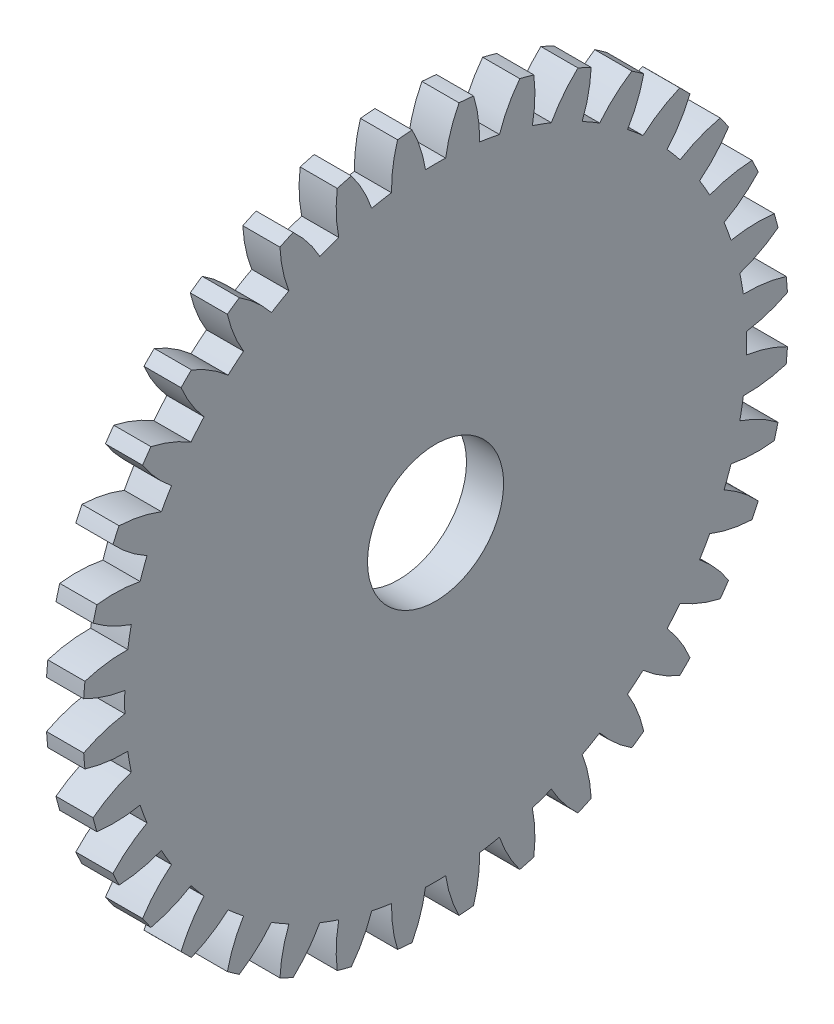
SolidWorks part; units mm, degrees
ref_plane "Plane1" through (0, 0, 0) normal (0, 0, 1) x (1, 0, 0)
ref_plane "Plane2" through (0, 0, 0) normal (0, 1, 0) x (1, 0, 0)
ref_plane "Plane3" through (0, 0, 0) normal (1, 0, 0) x (0, 0, -1)
other "Configuration Table"
sketch "HoldingSke" plane through (0, 0, 0) normal (0, 1, 0) x (1, 0, 0)
  line L0 (0, 0) -> (0.2697, -0.1959)
  line L1 (-15, 0) -> (100, 0) construction
  line L2 (0, 0) -> (-2.1039, 2.3779)
  line L3 (0, 0) -> (-11.863, 4.5341)
  line L4 (0, 0) -> (6.9867, 5.0761)
  line L5 (0, 0) -> (-46.8476, -17.4728)
  line L6 (0, 0) -> (-4.9738, -3.3558)
  line L7 (-2.1039, 2.3779) -> (8.6586, 51.2059)
  line L8 (-76.2, 54.61) -> (-72.9, 54.61)
  line L9 (-67.7845, 28.3722) -> (-49.3413, 33.142)
  line L10 (-76.2, 71.12) -> (104.1128, 71.12)
  line L11 (0, 0) -> (-6, 0)
  line L12 (-76.2, 101.6) -> (-76.093, 101.6)
  line L13 (24.9733, 27.94) -> (52.9518, 28.4284)
  line L14 (24.9733, 27.94) -> (24.9743, 27.94)
  line L15 (24.9733, 27.94) -> (100.4006, 29.5858)
  line L16 (-63.627, -3) -> (-12.827, -3)
  circle A0 centre (0, 0) radius 11
  circle A1 centre (0, 0) radius 37.5
  circle A2 centre (0, 0) radius 37.5
  circle A3 centre (0, 0) radius 11
  dimension "MHD" = 75
  dimension "Hub_dia" = 75
  dimension "Bore" = 22
  dimension "MBD" = 22
  dimension "Num_teeth" = 36
  dimension "Pitch" = 0.3333
  dimension "Overall_len" = 50
  dimension "Show_teeth" = 36
  dimension "Thickness" = 6
  dimension "OAL" = 50.0001
  dimension "T_dim" = 3.3
  dimension "Ap" = 14.5
  dimension "H" = 19.05
  dimension "Pitch_radius" = 180.3128
  dimension "Width" = 6
  dimension "Backlash" = 0.107
  dimension "Addendum_fac" = 1
  dimension "Dedendum_fac" = 1.25
  dimension "Clearance_fac" = 0.25
  dimension "Dedendum_add" = 0.001
  dimension "Module" = 3
sketch "BasProSke" plane through (0, 0, 0) normal (0, 1, 0) x (1, 0, 0)
  line L0 (-10, 0) -> (60, 0) construction
  line L1 (0, 0) -> (0, 57)
  line L2 (0, 0) -> (6, 0)
  line L3 (6, 0) -> (6, 57)
  line L4 (6, 57) -> (0, 57)
  dimension "Thickness" = 6
  dimension "Diameter" = 114
revolve "Base-Revolve" add sketch "BasProSke" angle 360 about L0
sketch "TooCutSke" plane through (0, 0, 0) normal (1, 0, 0) x (0, 0, -1)
  line L1 (0, 0) -> (0, 107) construction
  line L2 (0, 0) -> (-2.5427, 53.9401) construction
  line L3 (0, 0) -> (-9.4052, 107.5023) construction
  line L4 (-2.5427, 53.9401) -> (-4.7026, 53.7511) construction
  arc A0 (1.6311, 50.2225) -> (-1.6311, 50.2225) centre (0, 0) ccw
  arc A1 (3.8063, 56.8982) -> (-3.8063, 56.8982) centre (0, 0) ccw
  circle A2 centre (0, 0) radius 54 construction
  circle A3 centre (0, 0) radius 52.28 construction
  arc A4 (-1.6311, 50.2225) -> (-3.8063, 56.8982) centre (-22.9828, 46.9573) ccw
  arc A5 (3.8063, 56.8982) -> (1.6311, 50.2225) centre (22.9828, 46.9573) ccw
  dimension "Root_dia" = 100.498
  dimension "Overcut_dia" = 114.0508
  dimension "Pitch_dia" = 108
  dimension "Base_dia" = 104.5599
  dimension "Flank_rad" = 21.6
  dimension "Half_ang" = 5
  dimension "Half_CT" = 2.1682
extrude "ToothCut" cut sketch "TooCutSke" along normal through all
fillet "Breaks" [suppressed] radius 0.06
fillet "RootFillets" [suppressed] radius 0.751
pattern_circular "TeethCuts" count 36 every 10 about axis through (-10, 0, 0) along (1, 0, 0) of "ToothCut", "RootFillets", "Breaks"
sketch "HubNeaOneSke" plane through (0, 0, 0) normal (-1, 0, 0) x (0, 0, 1)
  circle A0 centre (0, 0) radius 37.5
  dimension "Diameter" = 75
extrude "HubNearOne" [suppressed] add sketch "HubNeaOneSke" along normal blind 44.0001
sketch "HubNeaBotSke" plane through (0, 0, 0) normal (-1, 0, 0) x (0, 0, 1)
  circle A0 centre (0, 0) radius 37.5
  dimension "Diameter" = 75
extrude "HubNearBoth" [suppressed] add sketch "HubNeaBotSke" along normal blind 22
ref_plane "FarPln" through (6, 0, 0) normal (1, 0, 0) x (0, 0, -1)
sketch "HubFarSke" plane through (6, 0, 0) normal (1, 0, 0) x (0, 0, -1)
  circle A0 centre (0, 0) radius 37.5
  dimension "Diameter" = 75
extrude "HubFar" [suppressed] add sketch "HubFarSke" along normal blind 22
sketch "BorSke" plane through (0, 0, 0) normal (1, 0, 0) x (0, 0, -1)
  circle A0 centre (0, 0) radius 11
  dimension "Diameter" = 22
extrude "Bore" cut sketch "BorSke" along normal mid plane 100.0001
sketch "KeySke" plane through (0, 0, 0) normal (1, 0, 0) x (0, 0, -1)
  line L0 (-4, 0) -> (-4, 14.3)
  line L1 (-4, 14.3) -> (4, 14.3)
  line L2 (4, 14.3) -> (4, 0)
  line L3 (0, 0) -> (0, 34) construction
  line L4 (-4, 0) -> (4, 0)
  dimension "Offset" = 14.3
  dimension "Width" = 8
extrude "Keyway" [suppressed] cut sketch "KeySke" along normal mid plane 100.0001
pattern_circular "Keyway2" [suppressed] count 2 every 90 about axis through (-10, 0, 0) along (1, 0, 0)
equation "' \"Module@HoldingSke\" = 6.35"
equation "' \"Num_teeth@HoldingSke\" = 12"
equation "' \"Ap@HoldingSke\" =  20"
equation "' \"Ap@HoldingSke\" = 20"
equation "' \"Width@HoldingSke\" = 0.5 * 25.4"
equation "' \"Hub_dia@HoldingSke\"= 1 * 25.4"
equation "' \"Hub_dia@HoldingSke\" = 1 * 25.4"
equation "' \"Overall_len@HoldingSke\" = 1.0 * 25.4"
equation "' \"Bore@HoldingSke\" = 0.75 * 25.4"
equation "' \"T_dim@HoldingSke\" = 0.1 * 25.4"
equation "' \"Width@KeySke\" = 0.25 * 25.4"
equation "' \"Show_teeth@HoldingSke\" = 13"
equation "' \"Backlash@HoldingSke\" = 0.009 * 25.4"
equation "' \"Addendum_fac@HoldingSke\" = 1.0"
equation "' \"Dedendum_fac@HoldingSke\" = 1.25"
equation "' \"Dedendum_add@HoldingSke\" = 0.00005 * 25.4"
equation "' \"Clearance_fac@HoldingSke\" = 0.25"
equation "\"Pitch@HoldingSke\" = 1 / \"Module@HoldingSke\""
equation "\"Overcut_dia@TooCutSke\" = (\"Num_teeth@HoldingSke\" + 2 * \"Addendum_fac@HoldingSke\") / \"Pitch@HoldingSke\" + 0.002 * 25.4"
equation "\"Pitch_dia@TooCutSke\" = \"Num_teeth@HoldingSke\" / \"Pitch@HoldingSke\""
equation "\"Base_dia@TooCutSke\" = \"Num_teeth@HoldingSke\" / \"Pitch@HoldingSke\" * cos((\"Ap@HoldingSke\"  * 3.14159265 / 180))"
equation "\"Root_dia@TooCutSke\" = (\"Num_teeth@HoldingSke\" + 2) / \"Pitch@HoldingSke\" - 2 * (\"Addendum_fac@HoldingSke\" + \"Dedendum_fac@HoldingSke\") / \"Pitch@HoldingSke\" - \"Dedendum_add@HoldingSke\" * 2"
equation "\"Half_ang@TooCutSke\" = 180 / \"Num_teeth@HoldingSke\""
equation "\"Half_CT@TooCutSke\" = \"Num_teeth@HoldingSke\" / \"Pitch@HoldingSke\" * sin((3.14159265 / 2 / \"Num_teeth@HoldingSke\")) / 2 - 7 * \"Backlash@HoldingSke\" / 4"
equation "\"Flank_rad@TooCutSke\" = \"Num_teeth@HoldingSke\" / \"Pitch@HoldingSke\" / 5"
equation "\"Radius@RootFillets\" = \"Clearance_fac@HoldingSke\" / \"Pitch@HoldingSke\" + \"Dedendum_add@HoldingSke\""
equation "\"Break_rad@Breaks\" = 0.02 / \"Pitch@HoldingSke\""
equation "\"Thickness@HoldingSke\" = \"Width@HoldingSke\""
equation "\"OAL@HoldingSke\" = \"Thickness@HoldingSke\""
equation "\"MHD@HoldingSke\" = (\"Num_teeth@HoldingSke\" + 2) / \"Pitch@HoldingSke\" - 2 * (\"Addendum_fac@HoldingSke\" + \"Dedendum_fac@HoldingSke\")  / \"Pitch@HoldingSke\" - \"Dedendum_add@HoldingSke\" * 2"
equation "\"MBD@HoldingSke\" = (\"Num_teeth@HoldingSke\" + 2) / \"Pitch@HoldingSke\" - 2 * (\"Addendum_fac@HoldingSke\" + \"Dedendum_fac@HoldingSke\")  / \"Pitch@HoldingSke\" - \"Dedendum_add@HoldingSke\" * 2 - 0.002 * 25.4"
equation "\"MHD@HoldingSke\" = ((sgn( \"MHD@HoldingSke\" - \"Hub_dia@HoldingSke\" )-1)*( \"MHD@HoldingSke\" - \"Hub_dia@HoldingSke\" ))/-2+ \"Hub_dia@HoldingSke\""
equation "\"MBD@HoldingSke\" = ((sgn( \"MBD@HoldingSke\" - \"Bore@HoldingSke\" )-1)*( \"MBD@HoldingSke\" - \"Bore@HoldingSke\" ))/-2+ \"Bore@HoldingSke\""
equation "\"OAL@HoldingSke\" = ((sgn( \"OAL@HoldingSke\" - \"Overall_len@HoldingSke\" )+1)*( \"OAL@HoldingSke\" - \"Overall_len@HoldingSke\" ))/2 + \"Overall_len@HoldingSke\" + 0.000002 * 25.4"
equation "\"Num_teeth@TeethCuts\" = int( \"Show_teeth@HoldingSke\" ) + 1"
equation "\"Num_teeth@TeethCuts\" = ((sgn( \"Num_teeth@TeethCuts\" - \"Num_teeth@HoldingSke\" )-1)*( \"Num_teeth@TeethCuts\" - \"Num_teeth@HoldingSke\" ))/-2+ \"Num_teeth@HoldingSke\""
equation "\"Num_teeth@TeethCuts\" = ((sgn( \"Num_teeth@TeethCuts\" - 2.0)+1)*( \"Num_teeth@TeethCuts\" - 2.0))/2 +2.0"
equation "\"Angle@TeethCuts\" = 360.0 / \"Num_teeth@HoldingSke\""
equation "\"Diameter@BasProSke\" = (\"Num_teeth@HoldingSke\" + 2 * \"Addendum_fac@HoldingSke\") / \"Pitch@HoldingSke\""
equation "\"Thickness@BasProSke\"  = \"Thickness@HoldingSke\""
equation "' \"Fillet_rad@BasProSke\" =  \"Thickness@HoldingSke\" * 0.05"
equation "' \"Fillet_rad@BasProSke\" = \"Thickness@HoldingSke\" * 0.05"
equation "\"MHD@HoldingSke\" = ((sgn( \"MHD@HoldingSke\" - \"Root_dia@TooCutSke\" )-1)*( \"MHD@HoldingSke\" - \"Root_dia@TooCutSke\" ))/-2+ \"Root_dia@TooCutSke\""
equation "\"Diameter@HubNeaOneSke\" = \"MHD@HoldingSke\""
equation "\"Length@HubNearOne\" = \"OAL@HoldingSke\" - \"Thickness@BasProSke\""
equation "\"Diameter@HubNeaBotSke\" = \"MHD@HoldingSke\""
equation "\"Length@HubNearBoth\" = ( \"OAL@HoldingSke\" - \"Thickness@BasProSke\" ) / 2.0"
equation "\"Thickness@FarPln\" = \"Thickness@BasProSke\""
equation "\"Diameter@HubFarSke\" = \"MHD@HoldingSke\""
equation "\"Length@HubFar\" = ( \"OAL@HoldingSke\" - \"Thickness@BasProSke\" ) / 2.0"
equation "\"Diameter@BorSke\" = \"MBD@HoldingSke\""
equation "\"D1@Bore\" = \"OAL@HoldingSke\" * 2.0"
equation "\"D1@Keyway\" = \"OAL@HoldingSke\" * 2.0"
equation "\"Offset@KeySke\" = \"T_dim@HoldingSke\" + \"MBD@HoldingSke\" / 2.0"
